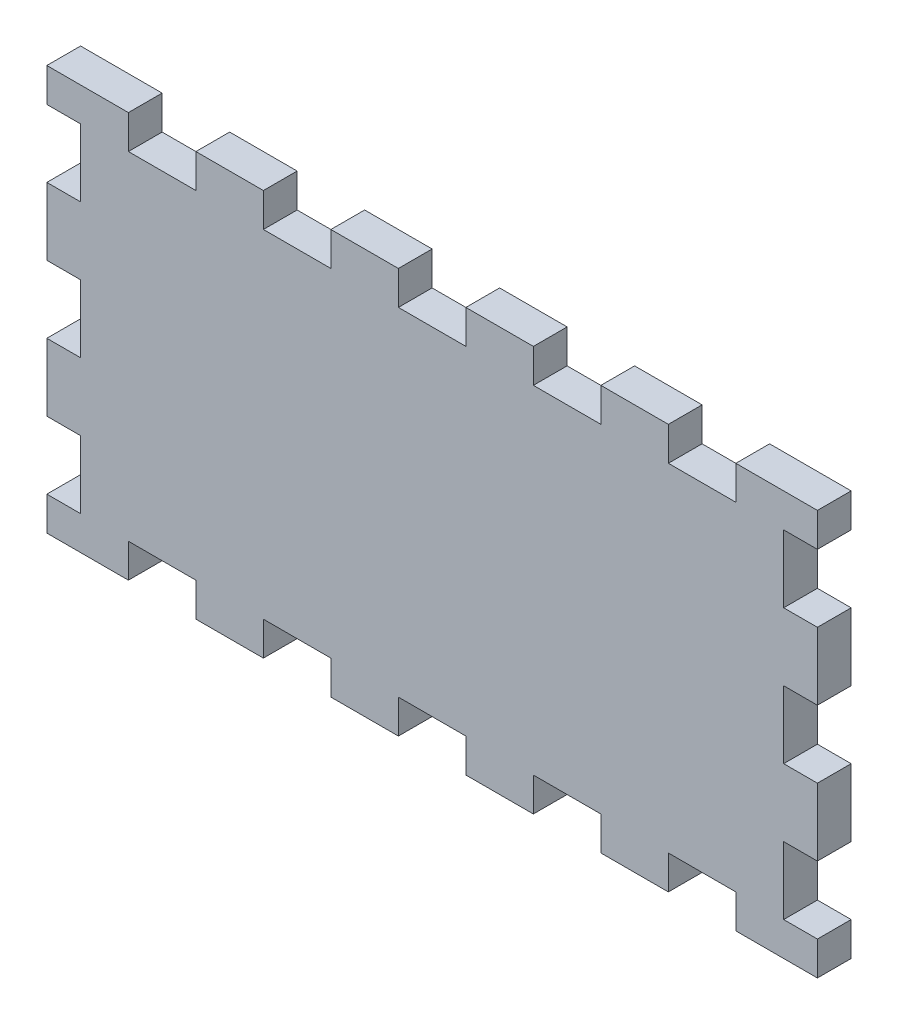
SolidWorks part; units mm, degrees
ref_plane "Front Plane" through (0, 0, 0) normal (0, 0, 1) x (1, 0, 0)
ref_plane "Top Plane" through (0, 0, 0) normal (0, 1, 0) x (1, 0, 0)
ref_plane "Right Plane" through (0, 0, 0) normal (1, 0, 0) x (0, 0, -1)
sketch "Sketch2" plane through (0, 0, 0) normal (0, 0, 1) x (1, 0, 0)
  line L0 (-68.5, 0) -> (-54, 0)
  line L1 (-54, 0) -> (-54, 6)
  line L2 (-54, 6) -> (-42, 6)
  line L3 (-42, 6) -> (-42, 0)
  line L4 (-42, 0) -> (-30, 0)
  line L5 (-30, 0) -> (-30, 6)
  line L6 (-30, 6) -> (-18, 6)
  line L7 (-18, 6) -> (-18, 0)
  line L8 (-18, 0) -> (-6, 0)
  line L9 (-6, 0) -> (-6, 6)
  line L10 (-6, 6) -> (6, 6)
  line L11 (6, 6) -> (6, 0)
  line L12 (6, 0) -> (18, 0)
  line L13 (18, 0) -> (18, 6)
  line L14 (18, 6) -> (30, 6)
  line L15 (30, 6) -> (30, 0)
  line L16 (30, 0) -> (42, 0)
  line L17 (42, 0) -> (42, 6)
  line L18 (42, 6) -> (54, 6)
  line L19 (54, 6) -> (54, 0)
  line L20 (54, 0) -> (68.5, 0)
  line L21 (68.5, 0) -> (68.5, 72)
  line L22 (-68.5, 0) -> (-68.5, 72)
  line L23 (-68.5, 36) -> (68.5, 36)
  line L24 (54, 72) -> (68.5, 72)
  line L25 (54, 66) -> (54, 72)
  line L26 (42, 66) -> (54, 66)
  line L27 (42, 72) -> (42, 66)
  line L28 (30, 72) -> (42, 72)
  line L29 (30, 66) -> (30, 72)
  line L30 (18, 66) -> (30, 66)
  line L31 (18, 72) -> (18, 66)
  line L32 (6, 72) -> (18, 72)
  line L33 (6, 66) -> (6, 72)
  line L34 (-6, 66) -> (6, 66)
  line L35 (-6, 72) -> (-6, 66)
  line L36 (-18, 72) -> (-6, 72)
  line L37 (-18, 66) -> (-18, 72)
  line L38 (-30, 66) -> (-18, 66)
  line L39 (-30, 72) -> (-30, 66)
  line L40 (-42, 72) -> (-30, 72)
  line L41 (-42, 66) -> (-42, 72)
  line L42 (-54, 66) -> (-42, 66)
  line L43 (-54, 72) -> (-54, 66)
  line L44 (-68.5, 72) -> (-54, 72)
  line M1 (-54, 0) -> (-54, 6)
  line M2 (-54, 6) -> (-62.5, 6)
  line M3 (-62.5, 6) -> (-62.5, 0)
  line M4 (-62.5, 0) -> (-54, 0)
  dimension "D1" = 72
extrude "Boss-Extrude1" add sketch "Sketch2" along normal blind 6 contours L44 L22 L23 L21 L24 L25 L26 L27 L28 L29 L30 L31 L32 L33 L34 L35 L36 L37 L38 L39 L40 L41 L42 L43 | L23 L22 L0 L2 L3 L4 L5 L6 L7 L8 L9 L10 L11 L12 L13 L14 L15 L16 L17 L18 L19 L20 L21 M3 M2 | M4 M1 M2 M3
sketch "Sketch3" plane through (0, 0, 6) normal (0, 0, 1) x (1, 0, 0)
  line L0 (-68.5, 0) -> (-68.5, 72) construction
  line L1 (-68.5, 6) -> (-62.5, 6)
  line L2 (-68.5, 6) -> (-68.5, 18)
  line L3 (-68.5, 18) -> (-62.5, 18)
  line L4 (-62.5, 6) -> (-62.5, 18)
  line L5 (62.5, 6) -> (62.5, 18)
  line L6 (62.5, 6) -> (68.5, 6)
  line L7 (68.5, 6) -> (68.5, 18)
  line L8 (62.5, 18) -> (68.5, 18)
  line L9 (62.5, 30) -> (62.5, 42)
  line L10 (62.5, 30) -> (68.5, 30)
  line L11 (68.5, 30) -> (68.5, 42)
  line L12 (62.5, 42) -> (68.5, 42)
  line L13 (62.5, 54) -> (62.5, 66)
  line L14 (62.5, 54) -> (68.5, 54)
  line L15 (68.5, 54) -> (68.5, 66)
  line L16 (62.5, 66) -> (68.5, 66)
  line L17 (-68.5, 30) -> (-68.5, 42)
  line L18 (-68.5, 30) -> (-62.5, 30)
  line L19 (-62.5, 30) -> (-62.5, 42)
  line L20 (-68.5, 42) -> (-62.5, 42)
  line L21 (-68.5, 54) -> (-68.5, 66)
  line L22 (-68.5, 54) -> (-62.5, 54)
  line L23 (-62.5, 54) -> (-62.5, 66)
  line L24 (-68.5, 66) -> (-62.5, 66)
  line L25 (68.5, 0) -> (68.5, 72) construction
  point P6 (-68.5, 36)
  point P8 (0, 0)
  point P28 (0, 0)
  point P29 (0, 0)
  line M26 (68.5, 0) -> (68.5, 72)
  line M48 (-68.5, 72) -> (-68.5, 0)
  dimension "D1" = 12
  dimension "D2" = 6
  dimension "D5" = 12
  dimension "D3" = 2
  dimension "D4" = 3
extrude "Cut-Extrude1" cut sketch "Sketch3" against normal blind 6 contours L24 L22 L23 M48 | L1 L4 L3 M48 | L12 L9 L10 M26 | L8 L5 L6 M26 | L17 L20 L19 L18 | L13 L16 L15 L14
